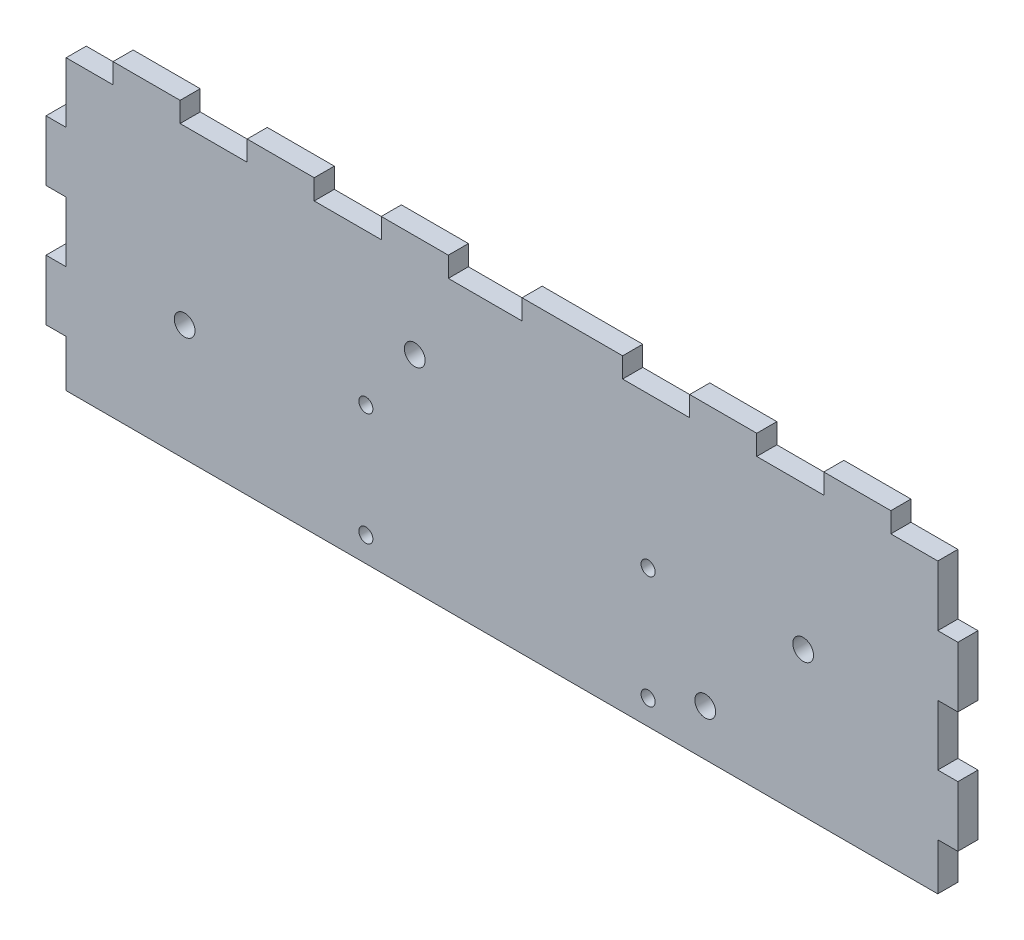
SolidWorks part; units mm, degrees
ref_plane "Front Plane" through (0, 0, 0) normal (0, 0, 1) x (1, 0, 0)
ref_plane "Top Plane" through (0, 0, 0) normal (0, 1, 0) x (1, 0, 0)
ref_plane "Right Plane" through (0, 0, 0) normal (1, 0, 0) x (0, 0, -1)
sketch "Sketch1" plane through (0, 0, 0) normal (0, 0, 1) x (1, 0, 0)
  line L4 (0, 0) -> (136, 0)
  line L5 (136, 0) -> (136, 46)
  line L6 (136, 46) -> (0, 46)
  line L7 (0, 46) -> (0, 0)
  line L8 (0, 0) -> (136, 0)
  line L9 (136, 0) -> (136, 46)
  line L10 (136, 46) -> (0, 46)
  line L11 (0, 46) -> (0, 0)
  dimension "D1" = 0
extrude "Boss-Extrude1" add sketch "Sketch1" along normal blind 3
sketch "Sketch4" plane through (0, 0, 3) normal (0, 0, 1) x (1, 0, 0)
  line L0 (136, 0) -> (136, 7) construction
  line L1 (136, 7) -> (133, 7) construction
  line L2 (133, 7) -> (133, 0) construction
  line L3 (133, 0) -> (136, 0) construction
  line L4 (133, 25) -> (133, 16) construction
  line L5 (133, 16) -> (136, 16) construction
  line L6 (136, 16) -> (136, 25) construction
  line L7 (136, 25) -> (133, 25) construction
  line L8 (136, 34) -> (136, 43) construction
  line L9 (133, 34) -> (136, 34) construction
  line L10 (133, 43) -> (133, 34) construction
  line L11 (136, 43) -> (133, 43) construction
  line L12 (126, 43) -> (136, 43) construction
  line L13 (126, 46) -> (126, 43) construction
  line L14 (136, 46) -> (126, 46) construction
  line L15 (136, 43) -> (136, 46) construction
  line L16 (40, 43) -> (50, 43) construction
  line L17 (50, 43) -> (50, 46) construction
  line L18 (50, 46) -> (40, 46) construction
  line L19 (40, 46) -> (40, 43) construction
  line L20 (60, 43) -> (71, 43) construction
  line L21 (71, 43) -> (71, 46) construction
  line L22 (71, 46) -> (60, 46) construction
  line L23 (60, 46) -> (60, 43) construction
  line L24 (86, 43) -> (96, 43) construction
  line L25 (96, 43) -> (96, 46) construction
  line L26 (96, 46) -> (86, 46) construction
  line L27 (86, 46) -> (86, 43) construction
  line L28 (106, 46) -> (106, 43) construction
  line L29 (106, 43) -> (116, 43) construction
  line L30 (116, 43) -> (116, 46) construction
  line L31 (116, 46) -> (106, 46) construction
  line L32 (0, 25) -> (0, 16) construction
  line L33 (0, 16) -> (3, 16) construction
  line L34 (3, 16) -> (3, 25) construction
  line L35 (3, 25) -> (0, 25) construction
  line L36 (0, 43) -> (10, 43) construction
  line L37 (10, 43) -> (10, 46) construction
  line L38 (10, 46) -> (0, 46) construction
  line L39 (0, 46) -> (0, 43) construction
  line L40 (0, 43) -> (0, 34) construction
  line L41 (0, 34) -> (3, 34) construction
  line L42 (3, 34) -> (3, 43) construction
  line L43 (3, 43) -> (0, 43) construction
  line L44 (30, 43) -> (30, 46) construction
  line L45 (30, 46) -> (20, 46) construction
  line L46 (20, 46) -> (20, 43) construction
  line L47 (20, 43) -> (30, 43) construction
  line L48 (0, 7) -> (0, 0) construction
  line L49 (0, 0) -> (3, 0) construction
  line L50 (3, 0) -> (3, 7) construction
  line L51 (3, 7) -> (0, 7) construction
  line L52 (136, 0) -> (136, 7)
  line L53 (136, 7) -> (133, 7)
  line L54 (133, 7) -> (133, 0)
  line L55 (133, 0) -> (136, 0)
  line L56 (133, 25) -> (133, 16)
  line L57 (133, 16) -> (136, 16)
  line L58 (136, 16) -> (136, 25)
  line L59 (136, 25) -> (133, 25)
  line L60 (136, 34) -> (136, 43)
  line L61 (133, 34) -> (136, 34)
  line L62 (133, 43) -> (133, 34)
  line L63 (136, 43) -> (133, 43)
  line L64 (126, 43) -> (136, 43)
  line L65 (126, 46) -> (126, 43)
  line L66 (136, 46) -> (126, 46)
  line L67 (136, 43) -> (136, 46)
  line L68 (40, 43) -> (50, 43)
  line L69 (50, 43) -> (50, 46)
  line L70 (50, 46) -> (40, 46)
  line L71 (40, 46) -> (40, 43)
  line L72 (60, 43) -> (71, 43)
  line L73 (71, 43) -> (71, 46)
  line L74 (71, 46) -> (60, 46)
  line L75 (60, 46) -> (60, 43)
  line L76 (86, 43) -> (96, 43)
  line L77 (96, 43) -> (96, 46)
  line L78 (96, 46) -> (86, 46)
  line L79 (86, 46) -> (86, 43)
  line L80 (106, 46) -> (106, 43)
  line L81 (106, 43) -> (116, 43)
  line L82 (116, 43) -> (116, 46)
  line L83 (116, 46) -> (106, 46)
  line L84 (0, 25) -> (0, 16)
  line L85 (0, 16) -> (3, 16)
  line L86 (3, 16) -> (3, 25)
  line L87 (3, 25) -> (0, 25)
  line L88 (0, 43) -> (10, 43)
  line L89 (10, 43) -> (10, 46)
  line L90 (10, 46) -> (0, 46)
  line L91 (0, 46) -> (0, 43)
  line L92 (0, 43) -> (0, 34)
  line L93 (0, 34) -> (3, 34)
  line L94 (3, 34) -> (3, 43)
  line L95 (3, 43) -> (0, 43)
  line L96 (30, 43) -> (30, 46)
  line L97 (30, 46) -> (20, 46)
  line L98 (20, 46) -> (20, 43)
  line L99 (20, 43) -> (30, 43)
  line L100 (0, 7) -> (0, 0)
  line L101 (0, 0) -> (3, 0)
  line L102 (3, 0) -> (3, 7)
  line L103 (3, 7) -> (0, 7)
  line M3 (0, 46) -> (0, 0)
  line M4 (0, 0) -> (136, 0)
  line M5 (136, 0) -> (136, 46)
  line M6 (136, 46) -> (0, 46)
extrude "Cut-Extrude1" cut sketch "Sketch4" against normal up to next contours L88 L89 M6 M3 | L93 L94 L88 M3 | L86 L87 L85 M3 | L102 L103 M3 M4 | L98 L99 L96 M6 | L71 L68 L69 M6 | L75 L72 L73 M6 | L79 L76 L77 M6 | L81 L82 L80 M6 | L65 L64 L63 M6 M5 | L63 L62 L61 M5 | L59 L56 L57 M5 | L53 L54 M4 M5
sketch "Sketch5" plane through (0, 0, 0) normal (0, 0, -1) x (-1, 0, 0)
  circle A0 centre (-89.8, 20.5) radius 1.05 construction
  circle A1 centre (-89.8, 3.7) radius 1.05 construction
  circle A2 centre (-47.7, 20.5) radius 1.05 construction
  circle A3 centre (-47.7, 3.7) radius 1.05 construction
  circle A4 centre (-89.8, 20.5) radius 1.05
  circle A5 centre (-89.8, 3.7) radius 1.05
  circle A6 centre (-47.7, 20.5) radius 1.05
  circle A7 centre (-47.7, 3.7) radius 1.05
  circle A8 centre (-20.6776, 17.3142) radius 1.55 construction
  circle A9 centre (-55, 30.6513) radius 1.55 construction
  circle A10 centre (-112.9261, 21.5412) radius 1.55 construction
  circle A11 centre (-98.3232, 6.9294) radius 1.55 construction
  circle A12 centre (-20.6776, 17.3142) radius 1.55
  circle A13 centre (-55, 30.6513) radius 1.55
  circle A14 centre (-112.9261, 21.5412) radius 1.55
  circle A15 centre (-98.3232, 6.9294) radius 1.55
extrude "Cut-Extrude2" cut sketch "Sketch5" against normal up to next
